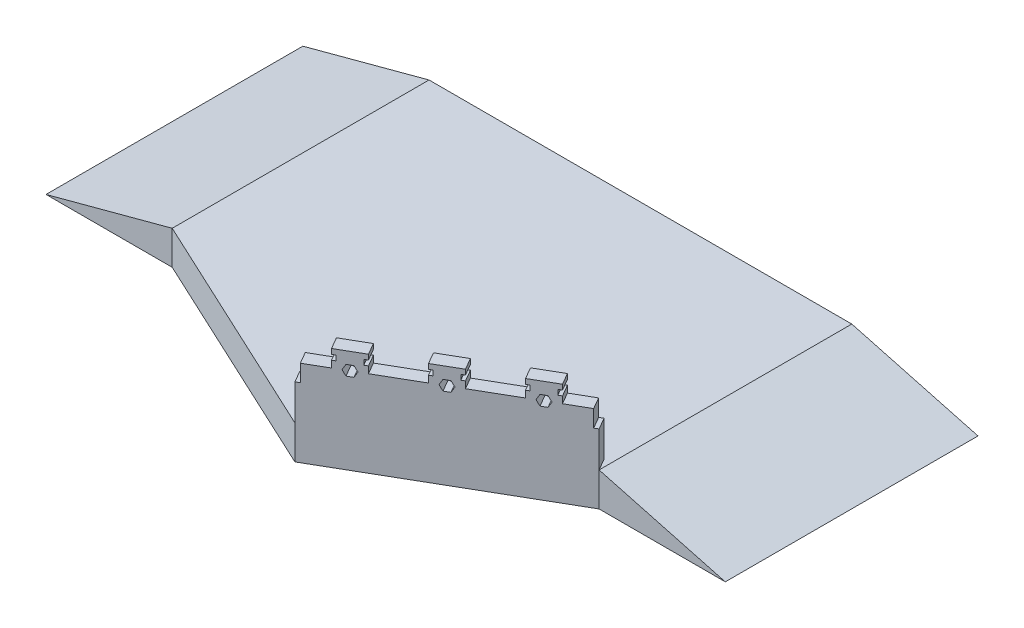
SolidWorks part; units mm, degrees
ref_plane "前视基准面" through (0, 0, 0) normal (0, 0, 1) x (1, 0, 0)
ref_plane "上视基准面" through (0, 0, 0) normal (0, 1, 0) x (1, 0, 0)
ref_plane "右视基准面" through (0, 0, 0) normal (1, 0, 0) x (0, 0, -1)
sketch "草图1" plane through (0, 0, 0) normal (0, 1, 0) x (1, 0, 0)
  line L0 (-1179.7501, -120.6383) -> (179.7115, -754.5657)
  line L1 (-1179.7501, 1398.3617) -> (1320.2499, 1398.3617)
  line L2 (-1179.7501, 1398.3617) -> (-1179.7501, -120.6383)
  line L4 (1320.2499, 1398.3617) -> (1320.2499, -96.0756)
  line L5 (179.7115, -754.5657) -> (1320.2499, -96.0756)
  point P0 (0, 0)
  dimension "D1" = 2500
  dimension "D2" = 1519
  dimension "D3" = 1500
  dimension "D4" = 115
  dimension "D5" = 120
extrude "凸台-拉伸1" add sketch "草图1" along normal blind 200
sketch "草图2" plane through (0, 0, -1398.3617) normal (0, 0, -1) x (-1, 0, 0)
  line L0 (-1320.2499, 200) -> (-1320.2499, 0)
  line L1 (-1320.2499, 0) -> (-2066.66, 0)
  line L2 (-2066.66, 0) -> (-1320.2499, 200)
  dimension "D1" = 15
extrude "凸台-拉伸2" add sketch "草图2" against normal up to vertex (1494.4373 mm away) up to point (1320.2499, 200, 96.0756)
sketch "草图3" plane through (0, 0, -1398.3617) normal (0, 0, -1) x (-1, 0, 0)
  line L0 (1179.7501, 200) -> (1179.7501, 0)
  line L1 (1179.7501, 0) -> (1926.1603, 0)
  line L2 (1926.1603, 0) -> (1179.7501, 200)
  dimension "D1" = 15
extrude "凸台-拉伸3" add sketch "草图3" against normal up to vertex (1519 mm away) up to point (-1179.7501, 200, 120.6383)
sketch "草图5" plane through (371.6644, 0, 643.7416) normal (0.5, 0, 0.866) x (0.866, 0, -0.5)
  line L0 (-221.6481, 200) -> (1095.3321, 200) construction
  line L1 (1095.3321, 200) -> (-221.6481, 200)
  line L2 (1095.3321, 200) -> (1095.3321, 410)
  line L3 (1095.3321, 410) -> (-221.6481, 410)
  line L4 (-221.6481, 200) -> (-221.6481, 410)
  line L5 (-221.6481, 200) -> (-221.6481, 0) construction
  line L6 (1095.3321, 200) -> (1095.3321, 0) construction
  dimension "D1" = 0
  dimension "D2" = 0
  dimension "D3" = 210
extrude "凸台-拉伸4" add sketch "草图5" against normal blind 80
sketch "草图6" plane through (371.6644, 0, 643.7416) normal (0.5, 0, 0.866) x (0.866, 0, -0.5)
  line L0 (1095.3321, 410) -> (-221.6481, 410) construction
  line L1 (-198.158, 410) -> (1071.842, 410)
  line L2 (-198.158, 410) -> (-198.158, 510)
  line L3 (-63.158, 610) -> (96.842, 610)
  line L4 (1071.842, 410) -> (1071.842, 510)
  line L6 (356.842, 610) -> (356.842, 580)
  line L7 (471.483, 510) -> (454.1625, 540)
  line L8 (454.1625, 540) -> (419.5215, 540)
  line L9 (419.5215, 540) -> (402.201, 510)
  line L10 (402.201, 510) -> (419.5215, 480)
  line L11 (419.5215, 480) -> (454.1625, 480)
  line L12 (454.1625, 480) -> (471.483, 510)
  line L13 (51.483, 510) -> (34.1625, 540)
  line L14 (34.1625, 540) -> (-0.4785, 540)
  line L15 (-0.4785, 540) -> (-17.799, 510)
  line L16 (-17.799, 510) -> (-0.4785, 480)
  line L17 (-0.4785, 480) -> (34.1625, 480)
  line L18 (34.1625, 480) -> (51.483, 510)
  line L19 (891.483, 510) -> (874.1625, 540)
  line L20 (874.1625, 540) -> (839.5215, 540)
  line L21 (839.5215, 540) -> (822.201, 510)
  line L22 (822.201, 510) -> (839.5215, 480)
  line L23 (839.5215, 480) -> (874.1625, 480)
  line L24 (874.1625, 480) -> (891.483, 510)
  line L25 (356.842, 580) -> (376.842, 580)
  line L26 (96.842, 510) -> (356.842, 510)
  line L27 (356.842, 510) -> (356.842, 550)
  line L28 (356.842, 550) -> (376.842, 550)
  line L29 (376.842, 580) -> (376.842, 550)
  line L30 (76.842, 580) -> (76.842, 550)
  line L31 (76.842, 550) -> (96.842, 550)
  line L32 (96.842, 550) -> (96.842, 510)
  line L33 (76.842, 580) -> (96.842, 580)
  line L34 (96.842, 580) -> (96.842, 610)
  line L35 (356.842, 610) -> (516.842, 610)
  line L36 (-63.158, 610) -> (-63.158, 580)
  line L37 (516.842, 610) -> (516.842, 580)
  line L38 (516.842, 580) -> (496.842, 580)
  line L39 (496.842, 580) -> (496.842, 550)
  line L40 (496.842, 550) -> (516.842, 550)
  line L41 (516.842, 550) -> (516.842, 510)
  line L42 (516.842, 510) -> (776.842, 510)
  line L43 (776.842, 510) -> (776.842, 550)
  line L44 (776.842, 550) -> (796.842, 550)
  line L45 (796.842, 550) -> (796.842, 580)
  line L46 (796.842, 580) -> (776.842, 580)
  line L47 (776.842, 580) -> (776.842, 610)
  line L48 (776.842, 610) -> (936.842, 610)
  line L49 (-63.158, 580) -> (-43.158, 580)
  line L50 (-43.158, 580) -> (-43.158, 550)
  line L51 (-43.158, 550) -> (-63.158, 550)
  line L52 (-63.158, 550) -> (-63.158, 510)
  line L53 (-63.158, 510) -> (-198.158, 510)
  line L54 (936.842, 610) -> (936.842, 580)
  line L55 (936.842, 580) -> (916.842, 580)
  line L56 (916.842, 580) -> (916.842, 550)
  line L57 (916.842, 550) -> (936.842, 550)
  line L58 (936.842, 550) -> (936.842, 510)
  line L59 (936.842, 510) -> (1071.842, 510)
  line L60 (-221.6481, 0) -> (1095.3321, 0) construction
  circle A0 centre (436.842, 510) radius 30 construction
  circle A1 centre (16.842, 510) radius 30 construction
  arc A2 (882.8228, 525) -> (830.8613, 525) centre (856.842, 510) ccw construction
  arc A3 (830.8613, 495) -> (882.8228, 495) centre (856.842, 510) ccw construction
  point P6 (436.842, 0)
  dimension "D3" = 80
  dimension "D4" = 60
  dimension "D5" = 60
  dimension "D6" = 60
  dimension "D7" = 420
  dimension "D8" = 420
  dimension "D9" = 80
  dimension "D10" = 80
  dimension "D11" = 80
  dimension "D12" = 20
  dimension "D13" = 30
  dimension "D14" = 30
  dimension "D15" = 30
  dimension "D16" = 80
  dimension "D17" = 80
  dimension "D18" = 30
  dimension "D19" = 20
  dimension "D20" = 20
  dimension "D21" = 160
  dimension "D22" = 80
  dimension "D23" = 20
  dimension "D24" = 160
  dimension "D25" = 80
  dimension "D26" = 1270
  dimension "D27" = 635
  dimension "D28" = 635
  dimension "D29" = 80
  dimension "D30" = 20
  dimension "D31" = 80
  dimension "D32" = 20
extrude "凸台-拉伸6" add sketch "草图6" against normal blind 80
